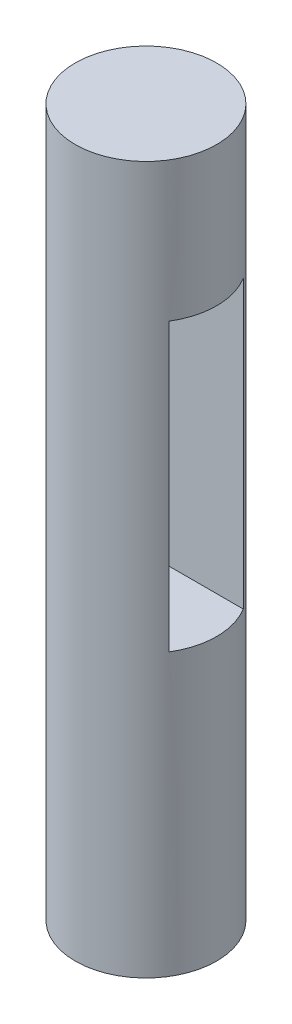
SolidWorks part; units mm, degrees
ref_plane "Front Plane" through (0, 0, 0) normal (0, 0, 1) x (1, 0, 0)
ref_plane "Top Plane" through (0, 0, 0) normal (0, 1, 0) x (1, 0, 0)
ref_plane "Right Plane" through (0, 0, 0) normal (1, 0, 0) x (0, 0, -1)
sketch "Sketch1" plane through (0, 0, 0) normal (0, 1, 0) x (1, 0, 0)
  circle A0 centre (0, 0) radius 5
  dimension "D1" = 10
extrude "Boss-Extrude1" add sketch "Sketch1" along normal blind 50
ref_plane "Plane1" through (5, 0, 0) normal (1, 0, 0) x (0, 0, -1)
sketch "Sketch2" plane through (5, 0, 0) normal (1, 0, 0) x (0, 0, -1)
  line L1 (-2.625, 19.875) -> (2.625, 19.875)
  line L2 (-2.625, 19.875) -> (-2.625, 40.125)
  line L3 (-2.625, 40.125) -> (2.625, 40.125)
  line L4 (2.625, 19.875) -> (2.625, 40.125)
  line L5 (-2.625, 19.875) -> (2.625, 40.125) construction
  line L6 (-2.625, 40.125) -> (2.625, 19.875) construction
  point P0 (0, 30)
  dimension "D1" = 5.25
  dimension "D2" = 20.25
  dimension "D3" = 30
extrude "Cut-Extrude1" cut sketch "Sketch2" against normal through all
